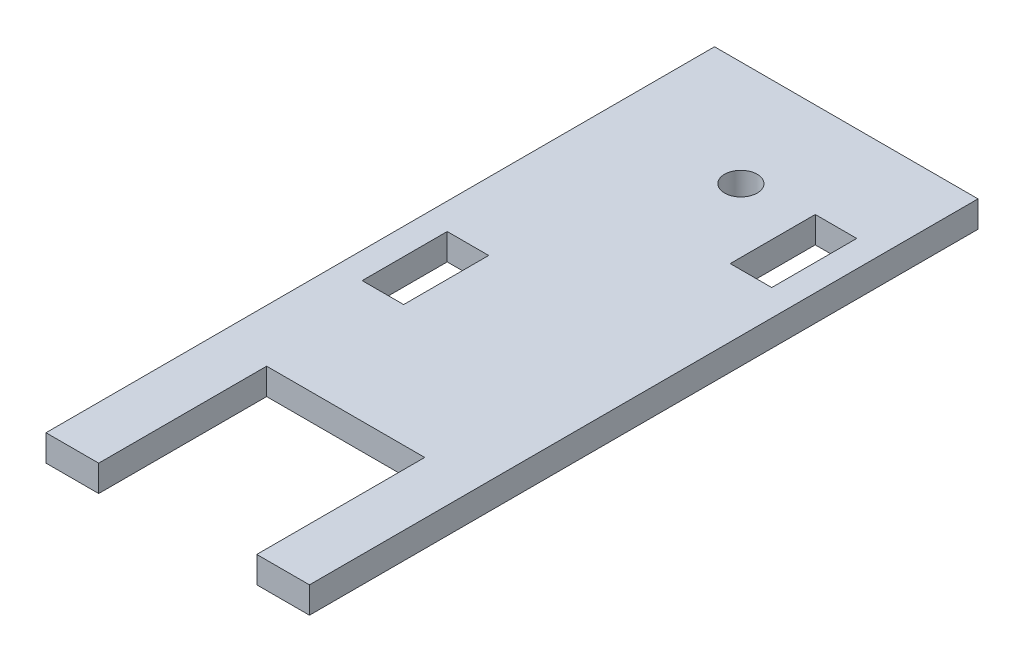
SolidWorks part; units mm, degrees
material "Maple"
ref_plane "Front Plane" through (0, 0, 0) normal (0, 0, 1) x (1, 0, 0)
ref_plane "Top Plane" through (0, 0, 0) normal (0, 1, 0) x (1, 0, 0)
ref_plane "Right Plane" through (0, 0, 0) normal (1, 0, 0) x (0, 0, -1)
sketch "Sketch1" plane through (0, 0, 0) normal (0, 1, 0) x (1, 0, 0)
  line L0 (0, 0) -> (127, 0)
  line L1 (0, 0) -> (0, 241.3)
  line L2 (127, 0) -> (127, 241.3)
  line L3 (0, 241.3) -> (127, 241.3)
  line L4 (63.5, 241.3) -> (63.5, 0) construction
  line L5 (127, 0) -> (101.6, 0)
  line L6 (127, 0) -> (127, -80.9625)
  line L7 (101.6, 0) -> (101.6, -80.9625)
  line L8 (127, -80.9625) -> (101.6, -80.9625)
  line L9 (25.4, 0) -> (0, 0)
  line L10 (25.4, 0) -> (25.4, -80.9625)
  line L11 (0, 0) -> (0, -80.9625)
  line L12 (25.4, -80.9625) -> (0, -80.9625)
  circle A0 centre (63.5, 190.5) radius 7.874
  dimension "D3" = 15.748
  dimension "D4" = 50.8
  dimension "D1" = 127
  dimension "D2" = 241.3
  dimension "D5" = 76.2
  dimension "D6" = 25.4
  dimension "D7" = 80.9625
extrude "Boss-Extrude1" add sketch "Sketch1" along normal blind 12.7 contours L3 L4 A0 L0 L2 | L4 L3 L1 L0 A0 | L8 L6 L0 L7 | L12 L10 L0 L11
ref_plane "Plane1" through (63.5, 0, 0) normal (-1, 0, 0) x (0, 0, 1)
sketch "Sketch2" plane through (0, 0, 0) normal (0, -1, 0) x (1, 0, 0)
  line L0 (0, -241.3) -> (127, -241.3) construction
  line L1 (114.3, -195.5532) -> (94.3, -195.5532)
  line L2 (114.3, -195.5532) -> (114.3, -154.5532)
  line L3 (114.3, -154.5532) -> (94.3, -154.5532)
  line L4 (94.3, -195.5532) -> (94.3, -154.5532)
  line L5 (127, 80.9625) -> (127, -241.3) construction
  dimension "D1" = 45.7468
  dimension "D2" = 12.7
  dimension "D3" = 41
  dimension "D4" = 20
extrude "Cut-Extrude1" cut sketch "Sketch2" against normal through all
sketch "Sketch3" plane through (0, 0, 0) normal (0, -1, 0) x (-1, 0, 0)
  line L0 (0, -80.9625) -> (0, 241.3) construction
  line L1 (-12.7, 58.7375) -> (-32.7, 58.7375)
  line L2 (-12.7, 58.7375) -> (-12.7, 99.7375)
  line L3 (-12.7, 99.7375) -> (-32.7, 99.7375)
  line L4 (-32.7, 58.7375) -> (-32.7, 99.7375)
  line L5 (-25.4, 0) -> (-101.6, 0) construction
  dimension "D1" = 12.7
  dimension "D2" = 58.7375
  dimension "D3" = 20
  dimension "D4" = 41
extrude "Cut-Extrude2" cut sketch "Sketch3" against normal through all
